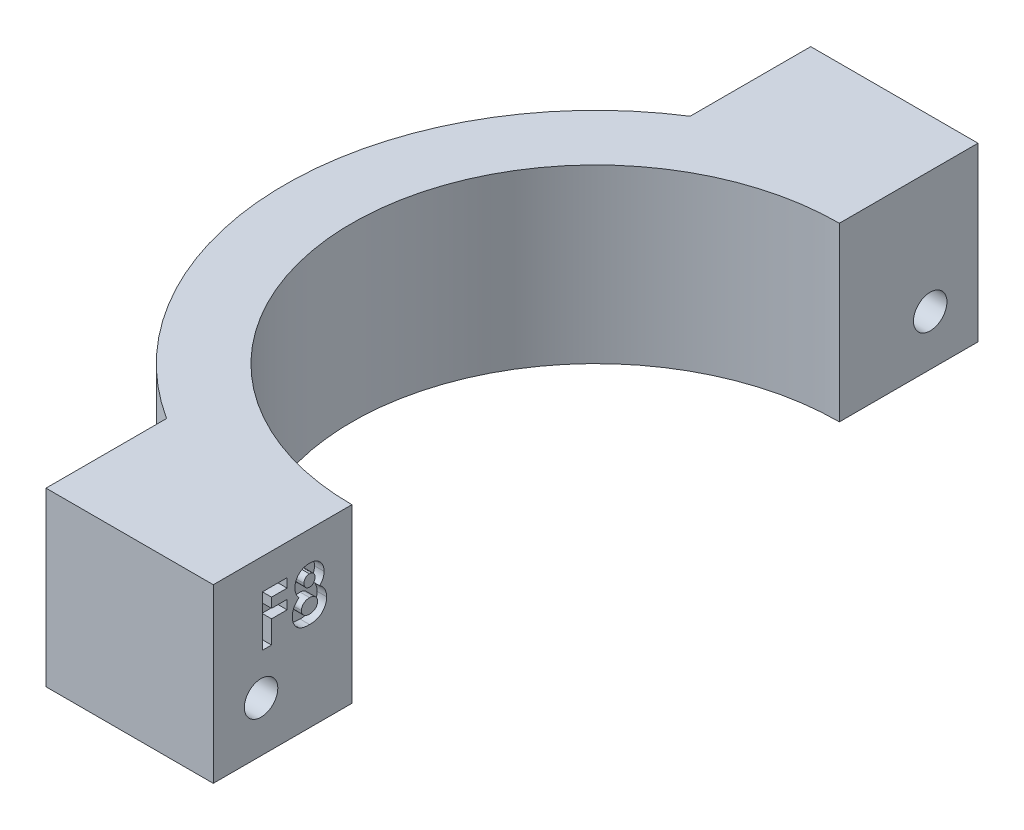
SolidWorks part; units mm, degrees
ref_plane "Front Plane" through (0, 0, 0) normal (0, 0, 1) x (1, 0, 0)
ref_plane "Top Plane" through (0, 0, 0) normal (0, 1, 0) x (1, 0, 0)
ref_plane "Right Plane" through (0, 0, 0) normal (1, 0, 0) x (0, 0, -1)
sketch "Sketch1" plane through (0, 0, 0) normal (0, 1, 0) x (1, 0, 0)
  line L0 (-46.9983, 32.5286) -> (-46.9983, -47.4714)
  line L1 (-46.9983, -47.4714) -> (-11.9983, -47.4714)
  line L2 (-11.9983, -47.4714) -> (-11.9983, -32.9714)
  line L3 (-46.9983, 32.5286) -> (-11.9983, 32.5286)
  line L4 (-11.9983, 32.5286) -> (-11.9983, 18.0286)
  line L5 (-29.4983, 32.5286) -> (-29.4983, 19.9147)
  line L6 (-29.4983, -47.4714) -> (-29.4983, -34.8576)
  arc A0 (-11.9983, 18.0286) -> (-11.9983, -32.9714) centre (-11.9983, -7.4714) ccw
  arc A1 (-11.9983, 25.0286) -> (-11.9983, -39.9714) centre (-11.9983, -7.4714) ccw
  dimension "D1" = 80
  dimension "D2" = 35
  dimension "D3" = 35
  dimension "D4" = 51
  dimension "D5" = 14.5
  dimension "D6" = 14.5
  dimension "D7" = 7
extrude "Boss-Extrude1" add sketch "Sketch1" along normal blind 18 contours A1 L4 L3 L5 | L4 A1 L2 A0 | A1 L6 L1 L2
sketch "Sketch2" plane through (-11.9983, 0, 0) normal (1, 0, 0) x (0, 0, -1)
  line L0 (-47.4714, 18) -> (-32.9714, 18) construction
  line L3 (32.5286, 18) -> (18.0286, 18) construction
  circle A0 centre (-42.4714, 5.25) radius 1.75
  circle A1 centre (27.5286, 5.25) radius 1.75
  dimension "D3" = 3.5
  dimension "D4" = 3.5
  dimension "D1" = 12.75
  dimension "D2" = 12.75
extrude "Cut-Extrude1" cut sketch "Sketch2" against normal through all
sketch "Sketch3" plane through (-11.9983, 0, 0) normal (1, 0, 0) x (0, 0, -1)
  text T0 "<b>F8</b>" font "Century Gothic" height in points 20
extrude "Cut-Extrude2" cut sketch "Sketch3" against normal blind 1
sketch "Sketch4" plane through (-29.4983, 0, 0) normal (-1, 0, 0) x (0, 0, 1)
  line L1 (-25.3918, 2.9011) -> (-24.4259, 5.926)
  line L2 (-24.4259, 5.926) -> (-26.5627, 8.275)
  line L3 (-26.5627, 8.275) -> (-29.6653, 7.5989)
  line L4 (-29.6653, 7.5989) -> (-30.6312, 4.574)
  line L5 (-30.6312, 4.574) -> (-28.4944, 2.225)
  line L6 (-28.4944, 2.225) -> (-25.3918, 2.9011)
  line L7 (44.7168, 3.0046) -> (45.5387, 6.0719)
  line L8 (45.5387, 6.0719) -> (43.2933, 8.3172)
  line L9 (43.2933, 8.3172) -> (40.2261, 7.4954)
  line L10 (40.2261, 7.4954) -> (39.4042, 4.4281)
  line L11 (39.4042, 4.4281) -> (41.6496, 2.1828)
  line L12 (41.6496, 2.1828) -> (44.7168, 3.0046)
  circle A0 centre (-27.5286, 5.25) radius 2.75 construction
  circle A1 centre (42.4714, 5.25) radius 2.75 construction
  dimension "D1" = 5.5
extrude "Cut-Extrude3" cut sketch "Sketch4" against normal blind 5
